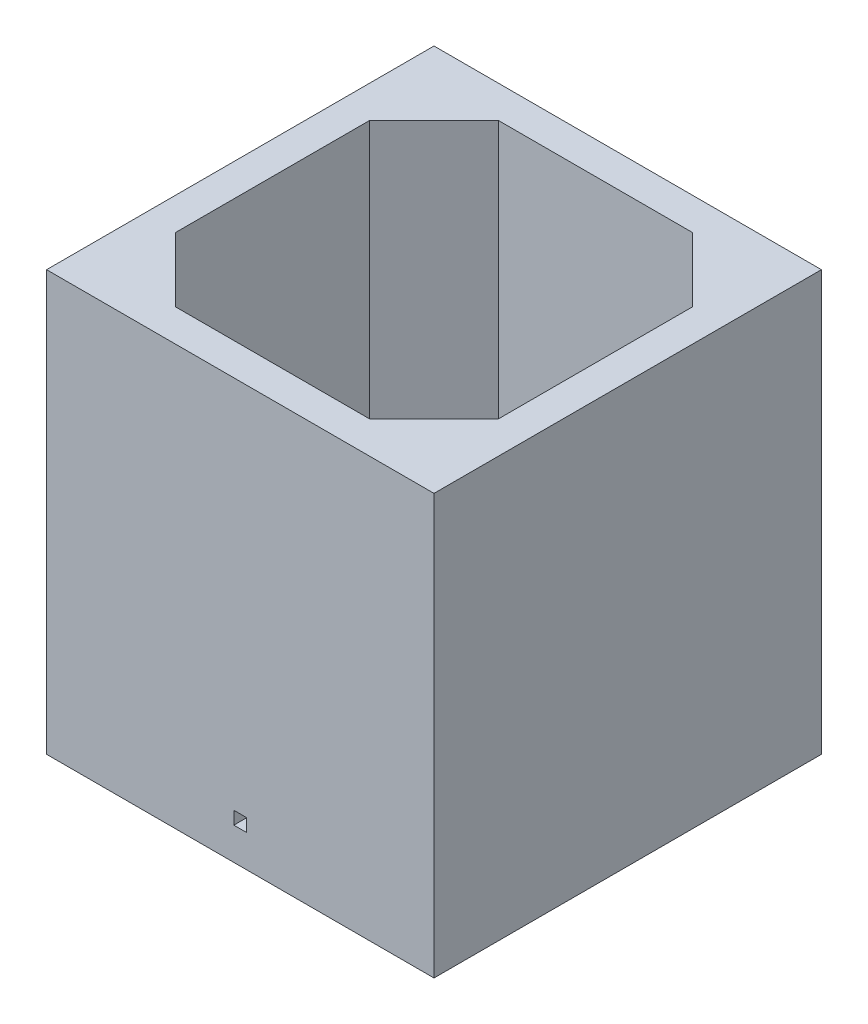
SolidWorks part; units mm, degrees
ref_plane "Front Plane" through (0, 0, 0) normal (0, 0, 1) x (1, 0, 0)
ref_plane "Top Plane" through (0, 0, 0) normal (0, 1, 0) x (1, 0, 0)
ref_plane "Right Plane" through (0, 0, 0) normal (1, 0, 0) x (0, 0, -1)
sketch "Sketch1" plane through (0, 0, 0) normal (0, 1, 0) x (1, 0, 0)
  line L1 (-25, -25) -> (25, -25)
  line L2 (-25, -25) -> (-25, 25)
  line L3 (-25, 25) -> (25, 25)
  line L4 (25, -25) -> (25, 25)
  line L5 (-25, -25) -> (25, 25) construction
  line L6 (-25, 25) -> (25, -25) construction
  line L7 (-30, -30) -> (30, -30)
  line L8 (-30, -30) -> (-30, 30)
  line L9 (-30, 30) -> (30, 30)
  line L10 (30, -30) -> (30, 30)
  line L11 (-30, -30) -> (30, 30) construction
  line L12 (-30, 30) -> (30, -30) construction
  point P0 (0, 0)
  point P6 (0, 0)
  dimension "D1" = 50
  dimension "D2" = 50
  dimension "D3" = 5
  dimension "D4" = 5
extrude "Boss-Extrude1" add sketch "Sketch1" along normal blind 60
sketch "Sketch2" plane through (0, 0, 0) normal (0, -1, 0) x (1, 0, 0)
  line L1 (-30, -30) -> (30, -30)
  line L2 (-30, -30) -> (-30, 30)
  line L3 (-30, 30) -> (30, 30)
  line L4 (30, -30) -> (30, 30)
  line L5 (-30, -30) -> (30, 30) construction
  line L6 (-30, 30) -> (30, -30) construction
  point P0 (0, 0)
extrude "Boss-Extrude2" add sketch "Sketch2" along normal blind 5
sketch "Sketch3" plane through (0, 0, -30) normal (0, 0, -1) x (-1, 0, 0)
  line L0 (-25, 0) -> (25, 0) construction
  line L1 (-25, 60) -> (-25, 0) construction
  circle A0 centre (0, 2.5) radius 1.25
  circle A1 centre (0, 8.1) radius 1.25
  dimension "D1" = 2.5
  dimension "D5" = 2.5
  dimension "D2" = 2.5
  dimension "D3" = 25
  dimension "D4" = 5.6
extrude "Cut-Extrude1" cut sketch "Sketch3" against normal up to surface (5 mm away) up to face at (0, 30, -25)
sketch "Sketch4" plane through (0, 0, -30) normal (0, 0, -1) x (-1, 0, 0)
  line L0 (0, 8.1) -> (-15.9728, 8.1) construction
  circle A0 centre (-13.1765, 8.1) radius 1.25
  dimension "D1" = 2.5
extrude "Cut-Extrude2" cut sketch "Sketch4" against normal up to next
chamfer "Chamfer1" distance 10 angle 45 4 edges at (-25, 30, 25) (-25, 30, -25) (25, 30, -25) (25, 30, 25)
sketch "Sketch6" plane through (0, 0, 30) normal (0, 0, 1) x (1, 0, 0)
  line L0 (-15, 0) -> (15, 0) construction
  line L1 (-1, 0) -> (1, 0)
  line L2 (-1, 0) -> (-1, 2)
  line L3 (-1, 2) -> (1, 2)
  line L4 (1, 0) -> (1, 2)
  point P6 (1, 1)
  dimension "D1" = 2
  dimension "D2" = 2
  dimension "D3" = 1
extrude "Cut-Extrude4" cut sketch "Sketch6" against normal up to next
